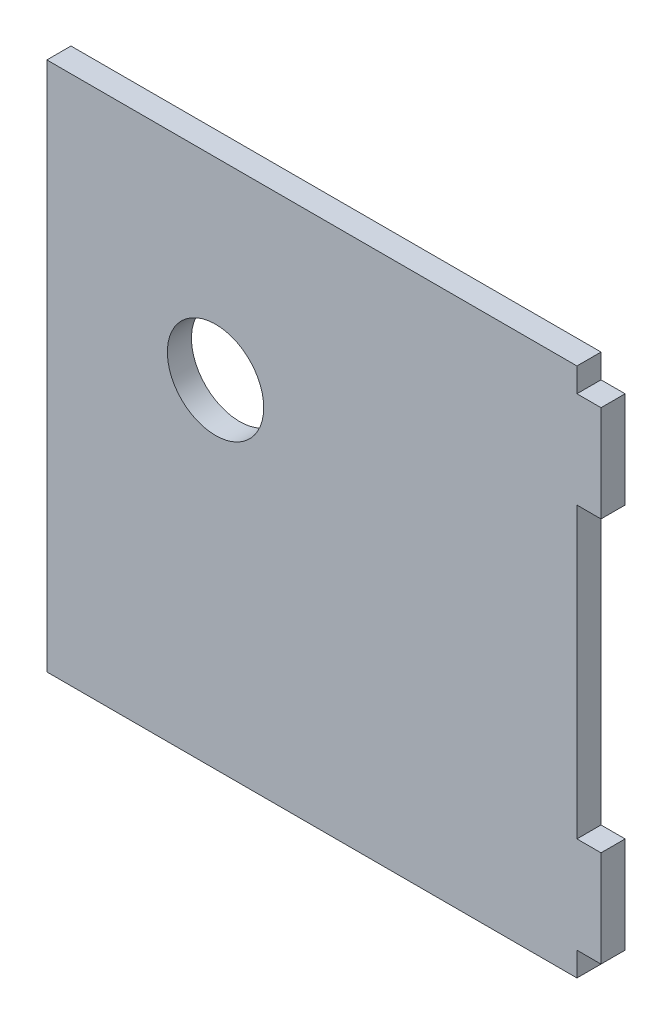
SolidWorks part; units mm, degrees
ref_plane "Front Plane" through (0, 0, 0) normal (0, 0, 1) x (1, 0, 0)
ref_plane "Top Plane" through (0, 0, 0) normal (0, 1, 0) x (1, 0, 0)
ref_plane "Right Plane" through (0, 0, 0) normal (1, 0, 0) x (0, 0, -1)
sketch "Sketch1" plane through (0, 0, 0) normal (0, 0, 1) x (1, 0, 0)
  line L0 (139.7, 133.35) -> (146.05, 133.35)
  line L1 (0, 0) -> (139.7, 0)
  line L2 (0, 0) -> (0, 139.7)
  line L3 (0, 139.7) -> (139.7, 139.7)
  line L4 (139.7, 0) -> (139.7, 6.35)
  line L5 (146.05, 133.35) -> (146.05, 107.95)
  line L6 (139.7, 107.95) -> (146.05, 107.95)
  line L7 (139.7, 6.35) -> (146.05, 6.35)
  line L8 (146.05, 6.35) -> (146.05, 31.75)
  line L9 (146.05, 31.75) -> (139.7, 31.75)
  line L10 (139.7, 107.95) -> (139.7, 31.75)
  line L11 (139.7, 133.35) -> (139.7, 139.7)
  circle A0 centre (44.45, 88.9) radius 12.7
extrude "Boss-Extrude1" add sketch "Sketch1" along normal blind 6.35
